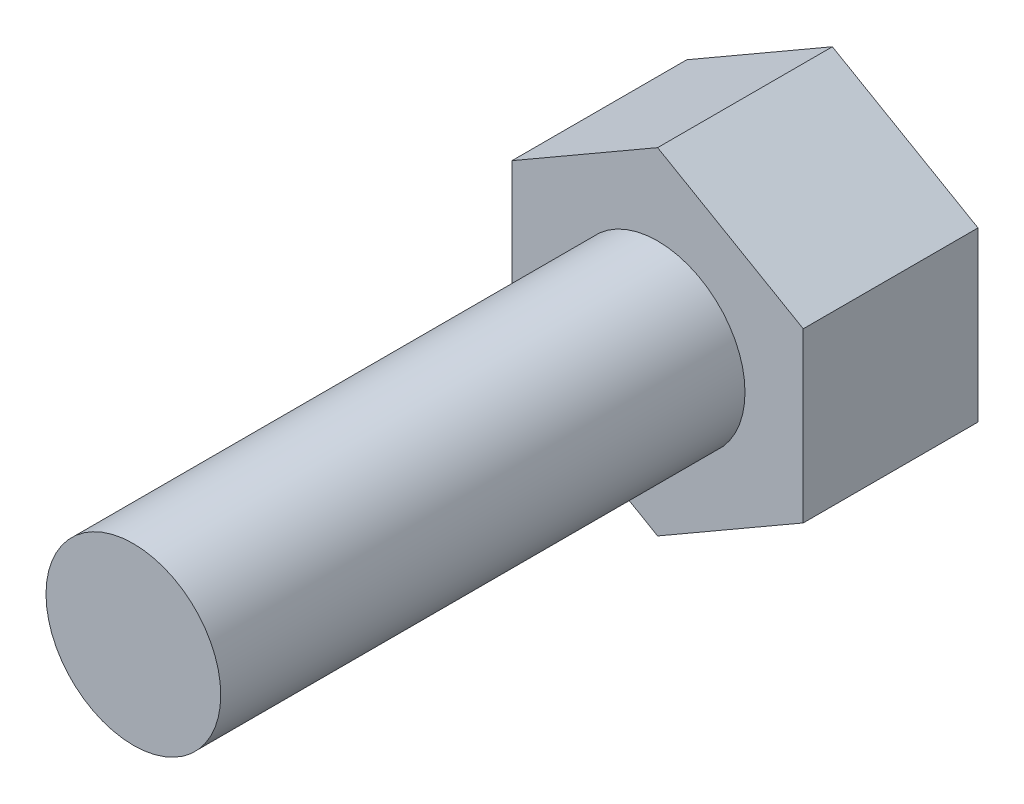
SolidWorks part; units mm, degrees
ref_plane "Front Plane" through (0, 0, 0) normal (0, 0, 1) x (1, 0, 0)
ref_plane "Top Plane" through (0, 0, 0) normal (0, 1, 0) x (1, 0, 0)
ref_plane "Right Plane" through (0, 0, 0) normal (1, 0, 0) x (0, 0, -1)
sketch "Sketch1" plane through (0, 0, 0) normal (0, 0, 1) x (1, 0, 0)
  circle A0 centre (-63.4948, 14.9787) radius 1.5
extrude "Boss-Extrude1" add sketch "Sketch1" along normal blind 9
sketch "Sketch2" plane through (0, 0, 0) normal (0, 0, -1) x (-1, 0, 0)
  line L1 (63.4948, 12.092) -> (65.9948, 13.5353)
  line L2 (65.9948, 13.5353) -> (65.9948, 16.4221)
  line L3 (65.9948, 16.4221) -> (63.4948, 17.8655)
  line L4 (63.4948, 17.8655) -> (60.9948, 16.4221)
  line L5 (60.9948, 16.4221) -> (60.9948, 13.5353)
  line L6 (60.9948, 13.5353) -> (63.4948, 12.092)
  circle A0 centre (63.4948, 14.9787) radius 2.5 construction
  dimension "D1" = 5
extrude "Boss-Extrude2" add sketch "Sketch2" along normal blind 3
